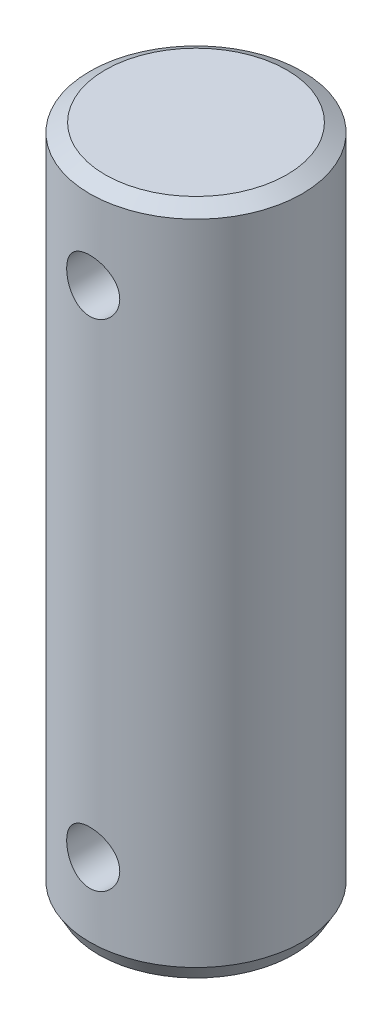
SolidWorks part; units mm, degrees
ref_plane "Front Plane" through (0, 0, 0) normal (0, 0, 1) x (1, 0, 0)
ref_plane "Top Plane" through (0, 0, 0) normal (0, 1, 0) x (1, 0, 0)
ref_plane "Right Plane" through (0, 0, 0) normal (1, 0, 0) x (0, 0, -1)
sketch "Sketch1" plane through (0, 0, 0) normal (0, 1, 0) x (1, 0, 0)
  circle A0 centre (0, 0) radius 6
  dimension "D1" = 12
extrude "Boss-Extrude1" add sketch "Sketch1" along normal mid plane 38
chamfer "Chamfer1" distance 0.5 angle 60 2 edges at (0, -19, 6) (0, 19, 6)
sketch "Sketch2" plane through (0, 0, 0) normal (0, 0, 1) x (1, 0, 0)
  line L0 (5.134, 19) -> (-5.134, 19) construction
  line L1 (-5.5, -19) -> (5.5, -19) construction
  circle A0 centre (0, 14) radius 1.5
  circle A1 centre (0, -14) radius 1.5
  point P4 (0, 10.6864)
  dimension "D1" = 3
  dimension "D2" = 3
  dimension "D3" = 5
  dimension "D4" = 5
extrude "Cut-Extrude1" cut sketch "Sketch2" against normal through all both and the other way through all
